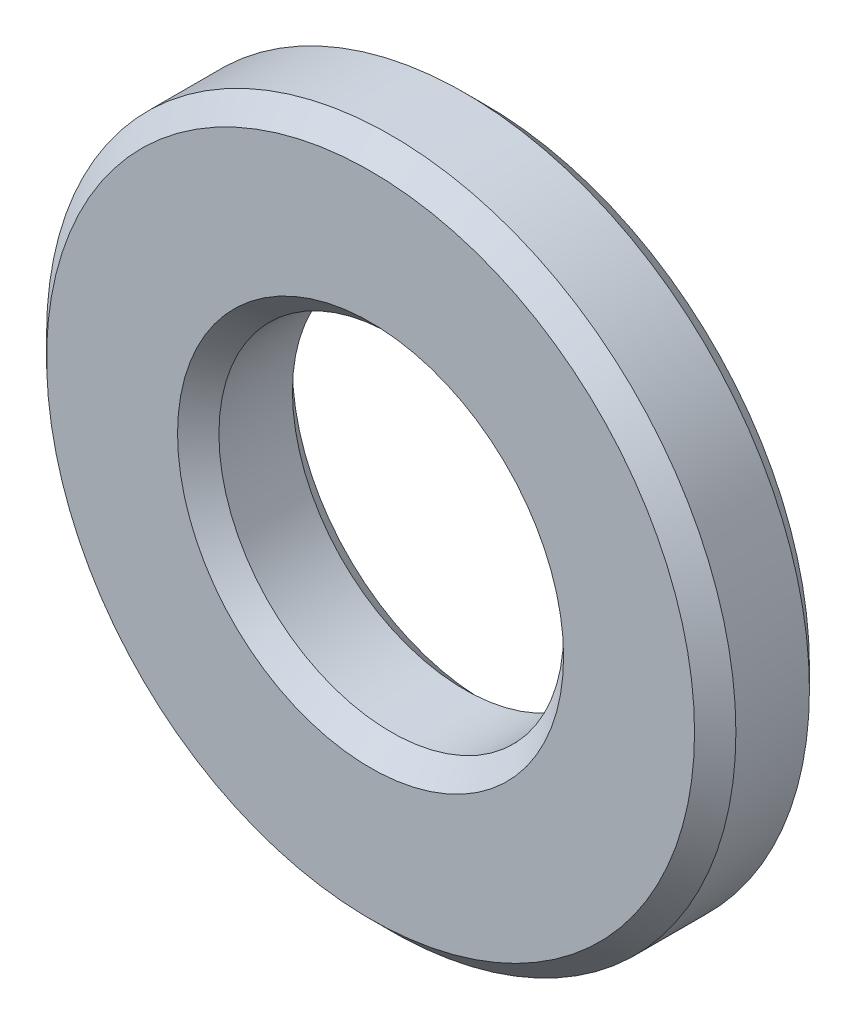
SolidWorks part; units mm, degrees
ref_plane "Front Plane" through (0, 0, 0) normal (0, 0, 1) x (1, 0, 0)
ref_plane "Top Plane" through (0, 0, 0) normal (0, 1, 0) x (1, 0, 0)
ref_plane "Right Plane" through (0, 0, 0) normal (1, 0, 0) x (0, 0, -1)
sketch "Sketch1" plane through (0, 0, 0) normal (0, 0, 1) x (1, 0, 0)
  circle A0 centre (0, 0) radius 19.05
  circle A1 centre (0, 0) radius 9.525
  dimension "OD" = 38.1
  dimension "ID" = 19.05
sketch "Sketch2" plane through (0, 0, 0) normal (1, 0, 0) x (0, 0, -1)
  line L0 (-3.175, 0) -> (3.175, 0) construction
  point P0 (3.175, 19.05)
  point P3 (0, 0)
  point P6 (-3.175, 19.05)
  point P7 (0, 19.05)
  dimension "Length" = 6.35
sketch "Sketch3" plane through (0, 0, 0) normal (0, 0, 1) x (1, 0, 0)
  circle A0 centre (0, 0) radius 19.05 construction
  circle A1 centre (0, 0) radius 9.525 construction
  circle A2 centre (0, 0) radius 19.05
  circle A3 centre (0, 0) radius 9.525
extrude "Boss-Extrude1" add sketch "Sketch3" against normal up to vertex (3.175 mm away) and the other way up to vertex (3.175 mm away) up to point (0, 0, -3.175) other way up to point (0, 0, 3.175)
chamfer "Chamfer1" distance 1.143 angle 45 4 edges at (19.05, 0, -3.175) (19.05, 0, 3.175) (9.525, 0, -3.175) (9.525, 0, 3.175)
sketch "Sketch4" plane through (0, 0, 0) normal (1, 0, 0) x (0, 0, -1)
  line L0 (2.032, 9.525) -> (-2.032, 9.525)
  line L1 (-2.032, -9.525) -> (2.032, -9.525)
  line L2 (-2.032, -9.525) -> (2.032, -9.525)
  line L3 (2.032, 9.525) -> (-2.032, 9.525)
equation "\"D1@Chamfer1\"=\"OD@Sketch1\"*.03"
